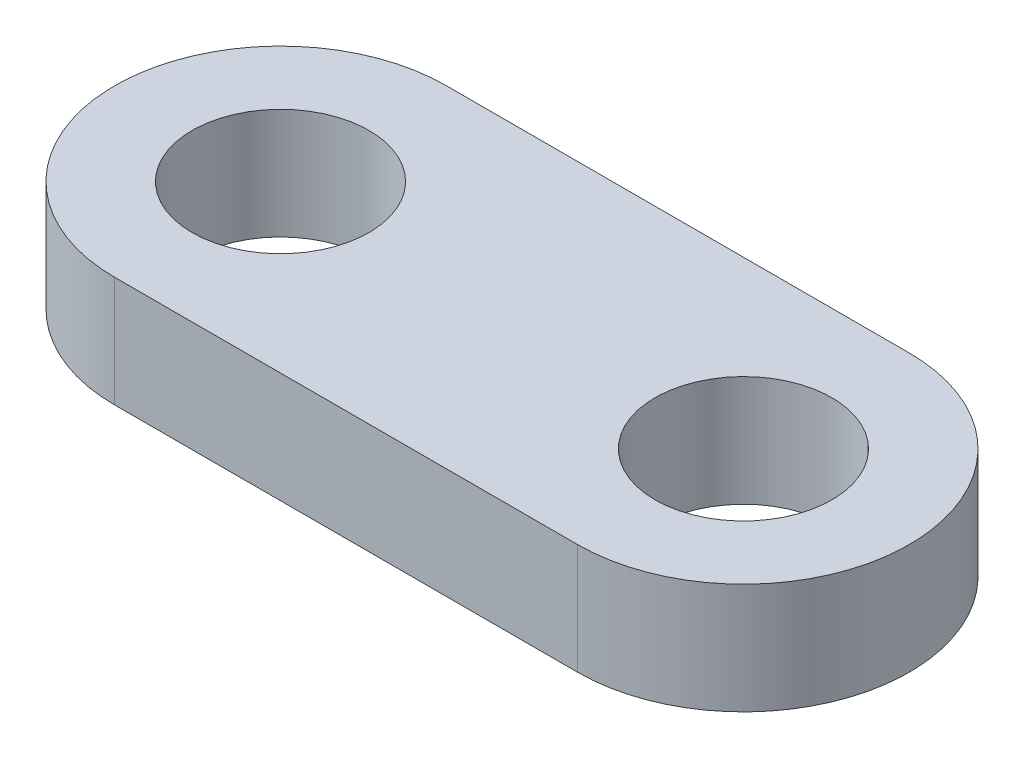
SolidWorks part; units mm, degrees
ref_plane "Front Plane" through (0, 0, 0) normal (0, 0, 1) x (1, 0, 0)
ref_plane "Top Plane" through (0, 0, 0) normal (0, 1, 0) x (1, 0, 0)
ref_plane "Right Plane" through (0, 0, 0) normal (1, 0, 0) x (0, 0, -1)
sketch "Sketch1" plane through (0, 0, 0) normal (0, 1, 0) x (1, 0, 0)
  line L0 (0, 7.5) -> (20.93, 7.5)
  line L1 (0, -7.5) -> (20.93, -7.5)
  arc A0 (0, 7.5) -> (0, -7.5) centre (0, 0) ccw
  arc A1 (20.93, -7.5) -> (20.93, 7.5) centre (20.93, 0) ccw
  circle A2 centre (20.93, 0) radius 4
  circle A3 centre (0, 0) radius 4
  dimension "D1" = 15
  dimension "D2" = 15
  dimension "D3" = 8
  dimension "D4" = 8
  dimension "D5" = 20.93
extrude "Boss-Extrude1" add sketch "Sketch1" along normal blind 5
